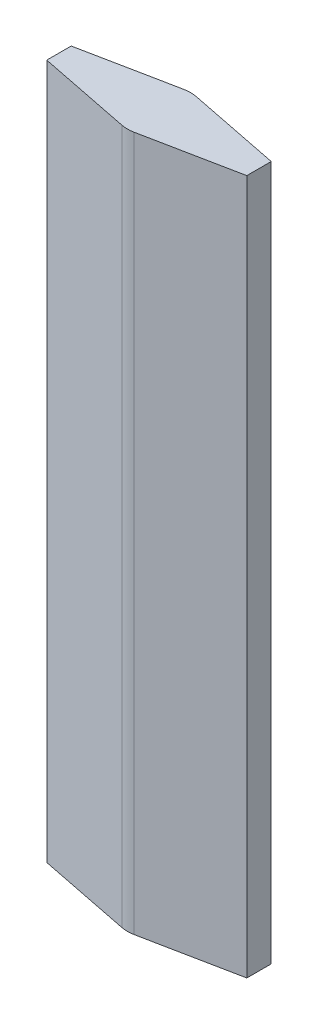
SolidWorks part; units mm, degrees
other "相机2"
other "相机3"
material "PEN"
ref_plane "前视基准面" through (0, 0, 0) normal (0, 0, 1) x (1, 0, 0)
ref_plane "上视基准面" through (0, 0, 0) normal (0, 1, 0) x (1, 0, 0)
ref_plane "右视基准面" through (0, 0, 0) normal (1, 0, 0) x (0, 0, -1)
sketch "草图4" plane through (0, 0, 0) normal (0, 1, 0) x (1, 0, 0)
  line L5 (-250, 0) -> (-9.604, -48.0496)
  line L7 (9.604, -48.0496) -> (250, 0)
  line L8 (250, 0) -> (9.604, 48.0496)
  line L9 (-9.604, 48.0496) -> (-250, 0)
  arc A2 (-9.604, -48.0496) -> (9.604, -48.0496) centre (0, 0) ccw
  arc A3 (9.604, 48.0496) -> (-9.604, 48.0496) centre (0, 0) ccw
sketch "草图5" plane through (0, 0, 0) normal (0, 1, 0) x (1, 0, 0)
  line L1 (190, 0) -> (190, -23.2102)
  line L2 (11.76, -58.8362) -> (190, -23.2102)
  line L3 (-190, -23.2102) -> (-11.76, -58.8362)
  line L4 (-190, 0) -> (-190, -23.2102)
  line L6 (-190, 0) -> (-190, 23.2102)
  line L17 (-11.76, 58.8362) -> (-190, 23.2102)
  line L18 (190, 23.2102) -> (11.76, 58.8362)
  line L19 (190, 0) -> (190, 23.2102)
  arc A0 (-11.76, -58.8362) -> (11.76, -58.8362) centre (0, 0) ccw
  arc A1 (11.76, 58.8362) -> (-11.76, 58.8362) centre (0, 0) ccw
extrude "凸台-拉伸1" add sketch "草图5" along normal mid plane 1320
